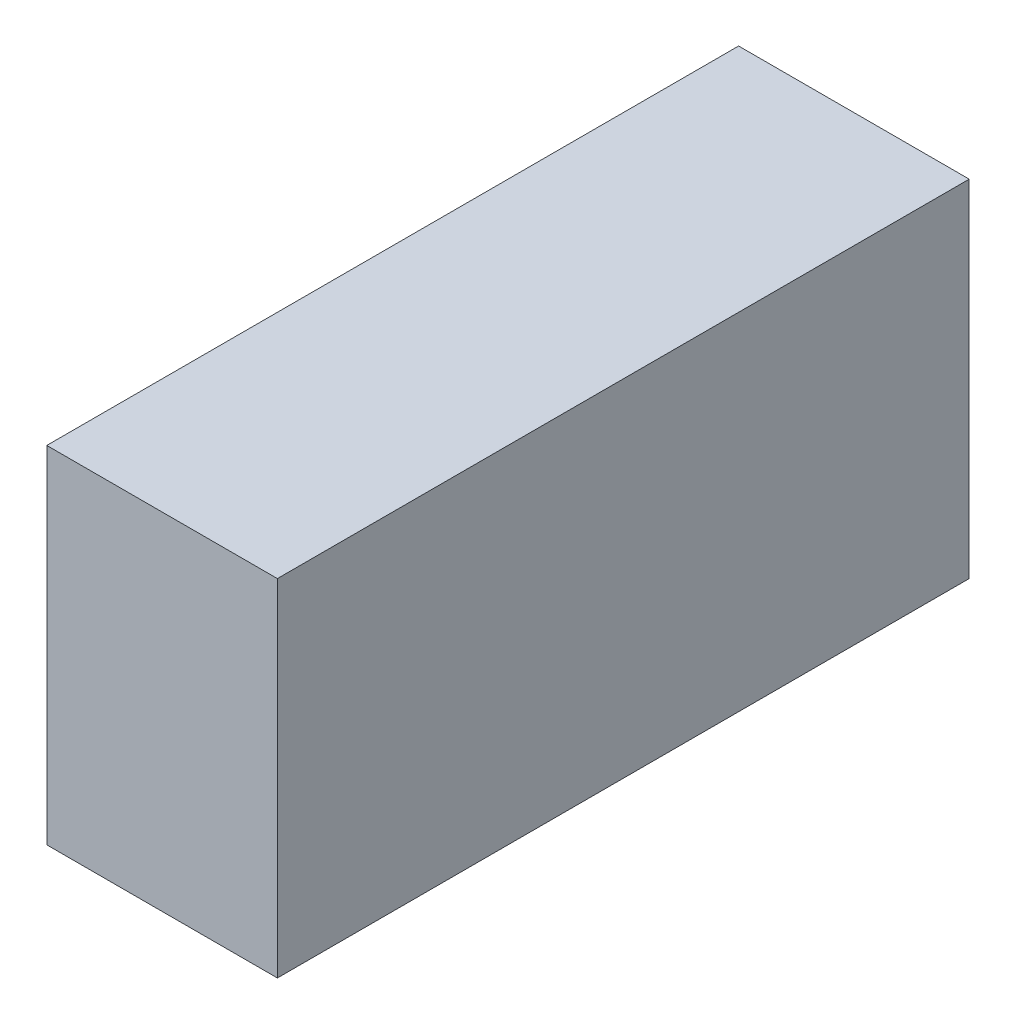
SolidWorks part; units mm, degrees
ref_plane "Front Plane" through (0, 0, 0) normal (0, 0, 1) x (1, 0, 0)
ref_plane "Top Plane" through (0, 0, 0) normal (0, 1, 0) x (1, 0, 0)
ref_plane "Right Plane" through (0, 0, 0) normal (1, 0, 0) x (0, 0, -1)
sketch "Sketch1" plane through (0, 0, 0) normal (1, 0, 0) x (0, 0, -1)
  line L1 (0, 0) -> (30, 0)
  line L2 (0, 0) -> (0, 15)
  line L3 (0, 15) -> (30, 15)
  line L4 (30, 0) -> (30, 15)
  dimension "D1" = 30
  dimension "D2" = 15
extrude "Boss-Extrude1" add sketch "Sketch1" along normal blind 10
